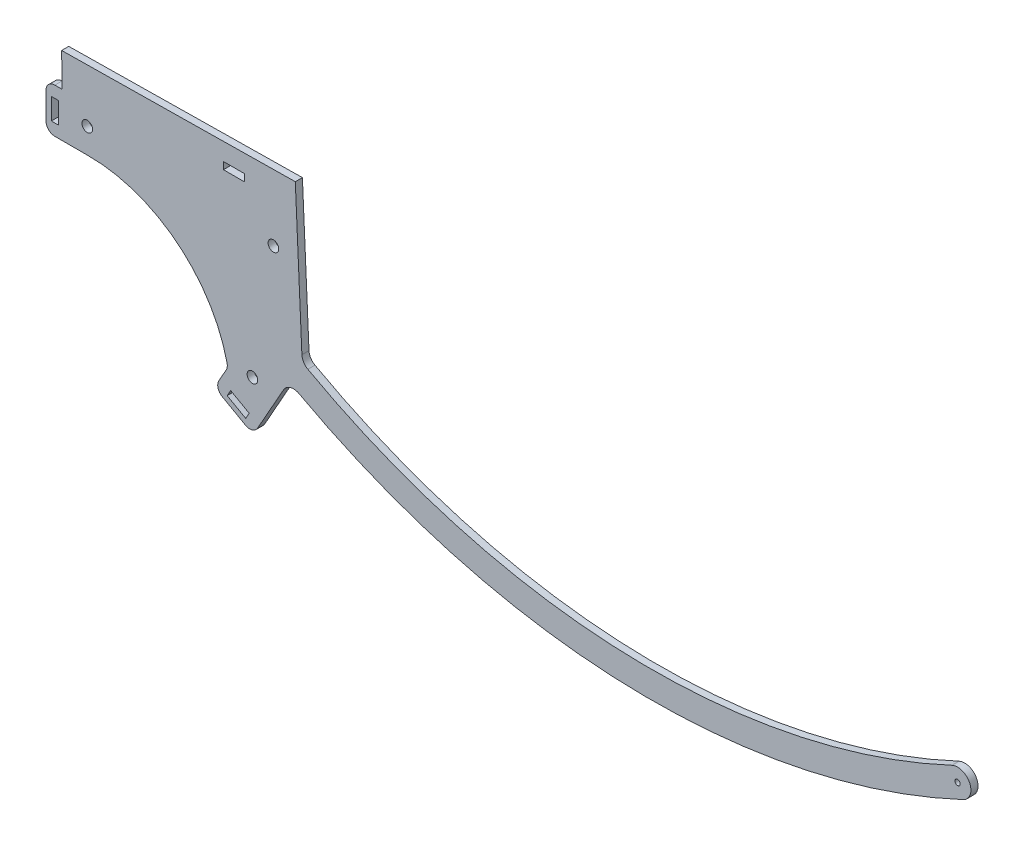
SolidWorks part; units mm, degrees
material "carbone"
ref_plane "Plan de face" through (0, 0, 0) normal (0, 0, 1) x (1, 0, 0)
ref_plane "Plan de dessus" through (0, 0, 0) normal (0, 1, 0) x (1, 0, 0)
ref_plane "Plan de droite" through (0, 0, 0) normal (1, 0, 0) x (0, 0, -1)
sketch "Esquisse1" plane through (0, 0, 0) normal (0, 0, 1) x (1, 0, 0)
  line L0 (-415, 0) -> (-385, 0) construction
  line L1 (-313.1067, -272.377) -> (70.5189, -272.377) construction
  line L2 (-313.1067, -272.377) -> (-15.9919, -246.3828) construction
  line L3 (-286.5711, -300.17) -> (75.0928, -268.5285) construction
  circle A0 centre (0, 0) radius 385 construction
  circle A1 centre (0, 0) radius 415 construction
  point P4 (-415, 0)
  point P5 (-192.2289, -367.7948)
  point P8 (-313.1067, -272.377)
  dimension "D1" = 830
  dimension "D2" = 30
  dimension "D3" = 430
  dimension "D4" = 154
  dimension "D5" = 5
  dimension "D6" = 30
sketch "Esquisse2" plane through (0, 0, 0) normal (0, 0, 1) x (1, 0, 0)
  line L0 (-317.1344, -294.0782) -> (-212.3002, -299.9748) construction
  line L1 (-203.4522, -361.7073) -> (0, 0) construction
  line L2 (-199.9716, -262.4789) -> (-196.0985, -348.6336)
  line L3 (-212.3002, -299.9748) -> (0, 0) construction
  line L4 (-313.1067, -272.377) -> (-15.9919, -246.3828) construction
  line L5 (-211.9204, -376.7625) -> (-203.4522, -361.7073)
  line L6 (180.3525, -357.0336) -> (187.1157, -370.4223)
  line L7 (-331.1331, -294.269) -> (-331.5419, -264.2717)
  line L8 (-331.5419, -264.2717) -> (-199.9716, -262.4789)
  line L9 (-317.1344, -294.0782) -> (0, 0) construction
  circle A0 centre (0, 0) radius 415 construction
  arc A1 (-203.4522, -361.7073) -> (187.1157, -370.4223) centre (0, 0) ccw
  arc A3 (-331.1331, -294.269) -> (-317.0174, -308.0777) centre (-317.1344, -294.0782) ccw
  arc A4 (-237.8584, -372.6061) -> (-211.9204, -376.7625) centre (-224.1226, -369.899) ccw
  circle A5 centre (-317.1344, -294.0782) radius 3
  circle A6 centre (-212.3002, -299.9748) radius 3
  circle A7 centre (-224.1226, -369.899) radius 3
  arc A8 (-317.0174, -308.0777) -> (-237.8584, -372.6061) centre (-316.3486, -388.0749) cw
  arc A9 (180.3525, -357.0336) -> (-196.0985, -348.6336) centre (0, 0) cw
  point P0 (-317.1344, -294.0782)
  point P1 (-224.1226, -369.899)
  point P2 (-212.3002, -299.9748)
  point P30 (-212.3002, -299.9748)
  dimension "D1" = 432.5
  dimension "D7" = 14
  dimension "D8" = 400
  dimension "D9" = 6
  dimension "D10" = 15
  dimension "D5" = 80
  dimension "D11" = 105
  dimension "D2" = 367.5
  dimension "D3" = 432.5
  dimension "D4" = 120
  dimension "D6" = 14
  dimension "D12" = 4
  dimension "D13" = 30
extrude "Boss.-Extru.1" add sketch "Esquisse2" along normal blind 4
sketch "Esquisse3" plane through (0, 0, 4) normal (0, 0, 1) x (1, 0, 0)
  line L0 (187.1157, -370.4223) -> (180.3525, -357.0336) construction
  line L1 (-199.9716, -262.4789) -> (-331.5419, -264.2717) construction
  line L2 (169.7604, -362.1897) -> (162.8772, -362.1897)
  line L3 (187.1157, -370.4223) -> (180.3525, -357.0336)
  line L4 (162.8772, -362.1897) -> (180.9651, -354.1521)
  line L5 (180.9651, -354.1521) -> (180.3525, -357.0336)
  line L6 (176.1264, -375.7718) -> (174.8535, -378.4751)
  line L7 (174.8535, -378.4751) -> (190.2868, -373.4747)
  line L8 (190.2868, -373.4747) -> (187.1157, -370.4223)
  arc A0 (183.7341, -363.728) -> (-310.433, -263.9841) centre (0, 0) cw construction
  circle A1 centre (172.9434, -368.9808) radius 1.5
  arc A2 (169.7604, -362.1897) -> (176.1264, -375.7718) centre (172.9434, -368.9808) cw
  arc A3 (-196.0985, -348.6336) -> (180.3525, -357.0336) centre (0, 0) ccw construction
  arc A4 (-203.4522, -361.7073) -> (187.1157, -370.4223) centre (0, 0) ccw construction
  dimension "D2" = 3
  dimension "D1" = 12
extrude "Enlèv. mat.-Extru.1" cut sketch "Esquisse3" against normal through all
fillet "Congé1" radius 6.5 2 edges at (-196.0985, -348.6336, 2) (-203.4522, -361.7073, 2)
sketch "Esquisse4" plane through (0, 0, 4) normal (0, 0, 1) x (1, 0, 0)
  line L0 (-211.9204, -376.7625) -> (-223.6864, -397.6805)
  line L1 (-211.9204, -376.7625) -> (-206.6143, -367.3289) construction
  line L2 (-223.6864, -397.6805) -> (-245.476, -385.4243)
  line L3 (-245.476, -385.4243) -> (-237.9656, -372.072)
  line L4 (-234.5812, -391.5524) -> (-232.1299, -387.1945) construction
  line L5 (-238.3399, -385.9962) -> (-227.8809, -391.8792)
  line L6 (-238.3399, -385.9962) -> (-236.3789, -382.5099)
  line L7 (-227.8809, -391.8792) -> (-225.9199, -388.3928)
  line L8 (-236.3789, -382.5099) -> (-225.9199, -388.3928)
  line L9 (-236.3789, -382.5099) -> (-227.8809, -391.8792) construction
  line L10 (-237.9656, -372.072) -> (-225.3743, -376.7625)
  line L11 (-225.3743, -376.7625) -> (-211.9204, -376.7625)
  line L12 (-316.3486, -308.0749) -> (-340.3486, -308.0749)
  line L13 (-340.3486, -308.0749) -> (-340.3486, -283.0749)
  line L14 (-340.3486, -283.0749) -> (-331.2857, -283.0749)
  line L15 (-331.5419, -264.2717) -> (-331.1331, -294.269) construction
  line L16 (-331.2857, -283.0749) -> (-316.3486, -308.0749)
  line L17 (-337.3486, -289.5749) -> (-337.3486, -301.5749)
  line L18 (-337.3486, -289.5749) -> (-333.3486, -289.5749)
  line L19 (-337.3486, -301.5749) -> (-333.3486, -301.5749)
  line L20 (-333.3486, -289.5749) -> (-333.3486, -301.5749)
  line L21 (-337.3486, -289.5749) -> (-333.3486, -301.5749) construction
  line L22 (-337.3486, -301.5749) -> (-333.3486, -289.5749) construction
  line L23 (-340.3486, -295.5749) -> (-335.3486, -295.5749) construction
  arc A0 (-237.8584, -372.6061) -> (-317.0174, -308.0777) centre (-316.3486, -388.0749) ccw construction
  point P12 (-232.1299, -387.1945)
  point P25 (-335.3486, -295.5749)
  dimension "D1" = 25
  dimension "D2" = 24
  dimension "D3" = 4
  dimension "D4" = 5
  dimension "D5" = 12
  dimension "D6" = 12
  dimension "D7" = 4
  dimension "D8" = 25
  dimension "D9" = 5
  dimension "D10" = 24
extrude "Boss.-Extru.2" add sketch "Esquisse4" against normal blind 4
fillet "Congé2" radius 5 5 edges at (-237.9656, -372.072, 2) (-245.476, -385.4243, 2) (-223.6864, -397.6805, 2) (-340.3486, -308.0749, 2) (-340.3486, -283.0749, 2)
sketch "Esquisse5" plane through (0, 0, 4) normal (0, 0, 1) x (1, 0, 0)
  line L0 (-196.2615, -345.0097) -> (-199.9716, -262.4789) construction
  line L1 (-240.45, -276.8679) -> (-228.45, -276.8679)
  line L2 (-240.45, -276.8679) -> (-240.45, -272.8679)
  line L3 (-240.45, -272.8679) -> (-228.45, -272.8679)
  line L4 (-228.45, -276.8679) -> (-228.45, -272.8679)
  line L5 (-240.45, -276.8679) -> (-228.45, -272.8679) construction
  line L6 (-240.45, -272.8679) -> (-228.45, -276.8679) construction
  line L7 (-199.9716, -262.4789) -> (-331.5419, -264.2717) construction
  point P0 (-234.45, -274.8679)
  dimension "D1" = 4
  dimension "D2" = 12
  dimension "D3" = 35
  dimension "D4" = 10
extrude "Enlèv. mat.-Extru.2" cut sketch "Esquisse5" against normal blind 4
